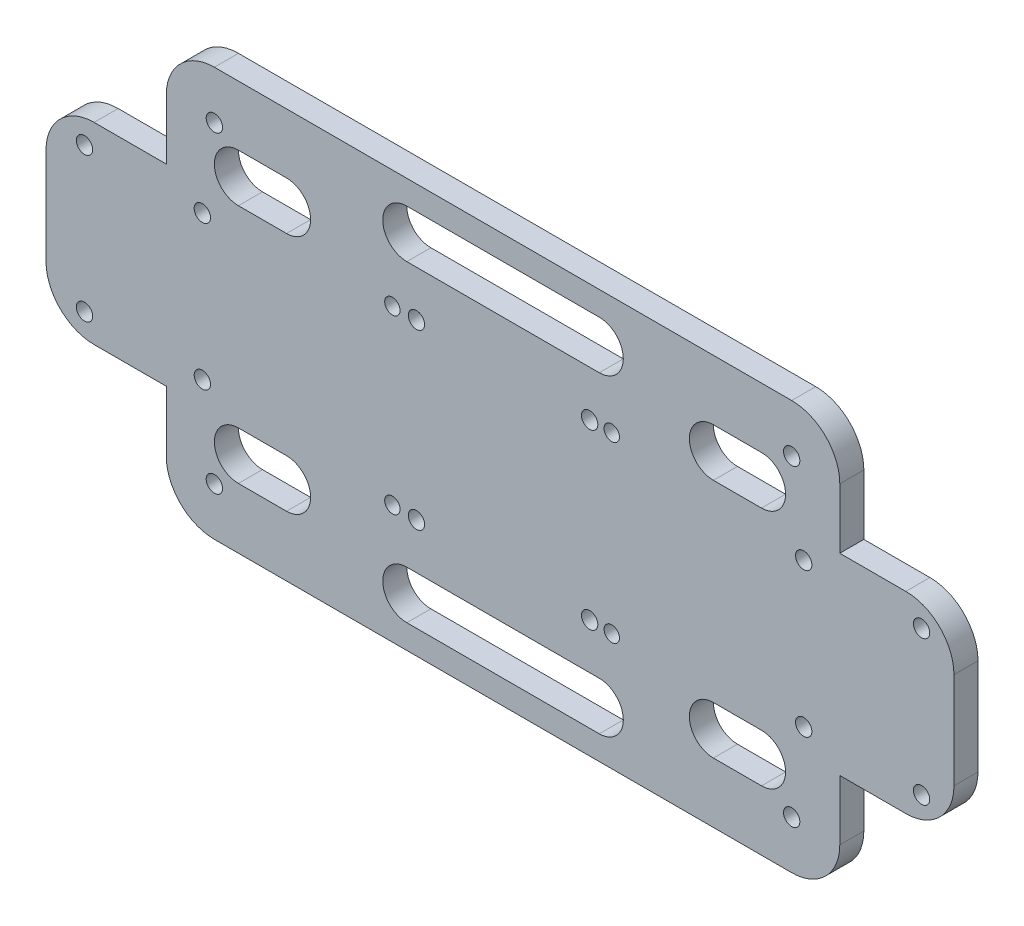
SolidWorks part; units mm, degrees
ref_plane "Front Plane" through (0, 0, 0) normal (0, 0, 1) x (1, 0, 0)
ref_plane "Top Plane" through (0, 0, 0) normal (0, 1, 0) x (1, 0, 0)
ref_plane "Right Plane" through (0, 0, 0) normal (1, 0, 0) x (0, 0, -1)
sketch "Sketch1" plane through (0, 0, 0) normal (0, 0, 1) x (1, 0, 0)
  line L1 (-60, 42.5) -> (60, 42.5)
  line L2 (-70, 32.5) -> (-70, 20.0641)
  line L3 (-60, -42.5) -> (60, -42.5)
  line L4 (70, 32.5) -> (70, 20)
  line L5 (-70, 42.5) -> (70, -42.5) construction
  line L6 (-66.3087, -40.2589) -> (70, 42.5) construction
  line L7 (-70, 42.5) -> (-60, 42.5)
  line L8 (-70, -19.9359) -> (-85, -19.9359)
  line L9 (-95, -9.9359) -> (-95, 10.0641)
  line L10 (-85, 20.0641) -> (-70, 20.0641)
  line L11 (70, -20) -> (70, -32.5)
  line L12 (-85, 20.0641) -> (-70, 20.0641)
  line L13 (-95, 10.0641) -> (-95, -17.1059)
  line L14 (-85, -19.9359) -> (-70, -19.9359)
  line L16 (-70, 42.5) -> (-70, 32.5)
  line L17 (-70, 32.5) -> (-60, 32.5)
  line L18 (-60, 42.5) -> (-60, 32.5)
  line L21 (-70, -19.9359) -> (-70, -32.5)
  line L24 (70, -20) -> (83.73, -20)
  line L25 (93.73, 10) -> (93.73, -10)
  line L26 (90.8011, -17.0711) -> (93.73, -20) construction
  line L28 (70, 20) -> (83.73, 20)
  line L29 (90.8011, 17.0711) -> (93.73, 20) construction
  arc A0 (-70, 32.5) -> (-60, 42.5) centre (-60, 32.5) cw
  arc A1 (70, 32.5) -> (60, 42.5) centre (60, 32.5) ccw
  arc A2 (70, -32.5) -> (60, -42.5) centre (60, -32.5) cw
  arc A3 (-60, -42.5) -> (-70, -32.5) centre (-60, -32.5) cw
  arc A4 (-95, 10.0641) -> (-85, 20.0641) centre (-85, 10.0641) cw
  arc A5 (-85, -19.9359) -> (-95, -9.9359) centre (-85, -9.9359) cw
  circle A6 centre (-87, 15) radius 1.7
  circle A7 centre (-62.5, 15) radius 1.7
  circle A8 centre (-62.5, -15) radius 1.7
  circle A9 centre (-87, -15) radius 1.7
  arc A10 (93.73, -10) -> (83.73, -20) centre (83.73, -10) cw
  arc A11 (93.73, 10) -> (83.73, 20) centre (83.73, 10) ccw
  circle A12 centre (62.5, 15) radius 1.7
  circle A13 centre (62.5, -15) radius 1.7
  circle A14 centre (87, -15) radius 1.7
  circle A15 centre (87, 15) radius 1.7
  circle A16 centre (-60, 32.5) radius 1.7
  circle A17 centre (60, 32.5) radius 1.7
  circle A18 centre (60, -32.5) radius 1.7
  circle A19 centre (-60, -32.5) radius 1.7
  point P0 (0, 0)
  point P25 (-95, 20.0641)
  point P28 (-95, -19.9359)
  dimension "D3" = 10
  dimension "D4" = 10
  dimension "D5" = 10
  dimension "D6" = 10
  dimension "D10" = 10
  dimension "D11" = 10
  dimension "D12" = 10
  dimension "D15" = 10
  dimension "D1" = 140
  dimension "D7" = 40
  dimension "D8" = 25
  dimension "D9" = 25
extrude "Boss-Extrude1" add sketch "Sketch1" along normal blind 5 contours A16 L18 A0 L17 | A16 L17 L2 L10 A4 L9 A5 L8 L21 A3 L3 A2 L11 L24 A10 L25 A11 L28 L4 A1 L1 L18 A19 A18 A17 A15 A14 A13 A12 A6 A7 A8 A9
sketch "Sketch2" plane through (0, 0, 0) normal (0, 0, 1) x (1, 0, 0)
  line L0 (0, 42.5) -> (0, 32.5) construction
  line L1 (-60, 42.5) -> (60, 42.5) construction
  line L2 (0, -42.5) -> (0, -32.5) construction
  line L3 (-60, -42.5) -> (60, -42.5) construction
  line L4 (-20, 32.5) -> (20, 32.5) construction
  line L5 (-95, 0.0641) -> (-50, 0.0641) construction
  line L6 (-20, 37.5) -> (20, 37.5)
  line L7 (-20, 27.5) -> (20, 27.5)
  line L8 (-20, -32.5) -> (20, -32.5) construction
  line L9 (-20, -27.5) -> (20, -27.5)
  line L10 (-20, -37.5) -> (20, -37.5)
  line L11 (-95, -9.9359) -> (-95, 10.0641) construction
  line L12 (-50, 0.0641) -> (-50, 25.0641) construction
  line L13 (93.73, 0) -> (48.73, 0) construction
  line L16 (93.73, 10) -> (93.73, -10) construction
  line L17 (-55, 25.0641) -> (-45, 25.0641) construction
  line L19 (-55, 30.0641) -> (-45, 30.0641)
  line L20 (-55, 20.0641) -> (-45, 20.0641)
  line L21 (-50, 0.0641) -> (-50, -24.9359) construction
  line L23 (-55, -24.9359) -> (-45, -24.9359) construction
  line L24 (48.73, 0) -> (48.73, -25) construction
  line L25 (-55, -19.9359) -> (-45, -19.9359)
  line L26 (-55, -29.9359) -> (-45, -29.9359)
  line L27 (48.73, 0) -> (48.73, 25) construction
  line L28 (43.73, 25) -> (53.73, 25) construction
  line L30 (43.73, 30) -> (53.73, 30)
  line L31 (43.73, 20) -> (53.73, 20)
  line L32 (43.73, -25) -> (53.73, -25) construction
  line L33 (43.73, -20) -> (53.73, -20)
  line L34 (43.73, -30) -> (53.73, -30)
  arc A0 (-20, 37.5) -> (-20, 27.5) centre (-20, 32.5) ccw
  arc A1 (20, 27.5) -> (20, 37.5) centre (20, 32.5) ccw
  arc A2 (-20, -27.5) -> (-20, -37.5) centre (-20, -32.5) ccw
  arc A3 (20, -37.5) -> (20, -27.5) centre (20, -32.5) ccw
  arc A4 (-55, 30.0641) -> (-55, 20.0641) centre (-55, 25.0641) ccw
  arc A5 (-45, 20.0641) -> (-45, 30.0641) centre (-45, 25.0641) ccw
  arc A8 (-55, -19.9359) -> (-55, -29.9359) centre (-55, -24.9359) ccw
  arc A9 (-45, -29.9359) -> (-45, -19.9359) centre (-45, -24.9359) ccw
  arc A10 (43.73, 30) -> (43.73, 20) centre (43.73, 25) ccw
  arc A11 (53.73, 20) -> (53.73, 30) centre (53.73, 25) ccw
  arc A12 (43.73, -20) -> (43.73, -30) centre (43.73, -25) ccw
  arc A13 (53.73, -30) -> (53.73, -20) centre (53.73, -25) ccw
  point P13 (0, 32.5)
  point P19 (0, -32.5)
  point P34 (-50, 25.0641)
  point P44 (-50, -24.9359)
  point P53 (48.73, 25)
  point P60 (48.73, -25)
extrude "Cut-Extrude4" cut sketch "Sketch2" along normal blind 5
sketch "Sketch3" plane through (0, 0, 0) normal (0, 0, 1) x (1, 0, 0)
  line L0 (0, 0) -> (-23, 0) construction
  line L1 (-25.5, 20.5) -> (25.5, 20.5)
  line L2 (-25.5, 20.5) -> (-25.5, -20.5)
  line L3 (-25.5, -20.5) -> (25.5, -20.5)
  line L4 (25.5, 20.5) -> (25.5, -20.5)
  line L5 (-25.5, 20.5) -> (25.5, -20.5) construction
  line L6 (-25.5, -20.5) -> (25.5, 20.5) construction
  line L11 (-23, 0) -> (-23, -17.8) construction
  line L12 (-23, 0) -> (-23, 18) construction
  line L13 (-23, 18) -> (22.6, 18) construction
  line L14 (22.6, 18) -> (22.6, -18.1686) construction
  line L20 (-21.5, 21.5) -> (21.5, -21.5) construction
  line L21 (-21.5, -21.5) -> (21.5, 21.5) construction
  circle A3 centre (-23, 18) radius 1.6
  circle A4 centre (-23, -17.8) radius 1.6
  circle A5 centre (22.6, 18) radius 1.6
  circle A6 centre (22.6, -18.1686) radius 1.6
  circle A7 centre (-18, 18) radius 1.7
  circle A8 centre (-18, -18) radius 1.7
  circle A9 centre (18, -18) radius 1.7
  circle A10 centre (18, 18) radius 1.7
  point P0 (0, 0)
  dimension "D1" = 43
extrude "Cut-Extrude7" cut sketch "Sketch3" along normal blind 5 contours A4 | A3 | A6 | A5 | A7 | A9 | A8 | A10
